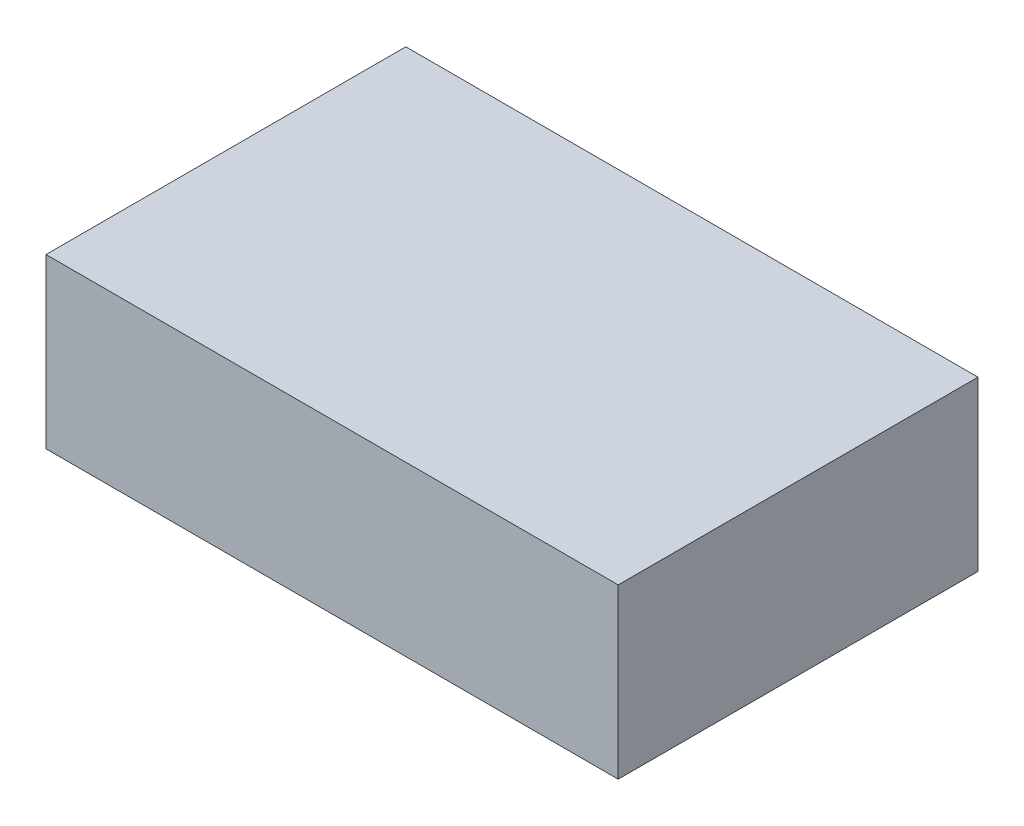
SolidWorks part; units mm, degrees
ref_plane "前视基准面" through (0, 0, 0) normal (0, 0, 1) x (1, 0, 0)
ref_plane "上视基准面" through (0, 0, 0) normal (0, 1, 0) x (1, 0, 0)
ref_plane "右视基准面" through (0, 0, 0) normal (1, 0, 0) x (0, 0, -1)
sketch "草图1" plane through (0, 0, 0) normal (0, 1, 0) x (1, 0, 0)
  line L1 (0, 0) -> (98.6, 0)
  line L2 (0, 0) -> (0, -62)
  line L3 (0, -62) -> (98.6, -62)
  line L4 (98.6, 0) -> (98.6, -62)
  dimension "D1" = 98.6
  dimension "D2" = 62
extrude "凸台-拉伸1" add sketch "草图1" along normal blind 29
ref_plane "基准面1" through (0, 0, 31) normal (0, 0, 1) x (1, 0, 0)
ref_plane "基准面2" through (0, 14.5, 0) normal (0, 1, 0) x (1, 0, 0)
ref_plane "基准面3" through (49.3, 0, 0) normal (1, 0, 0) x (0, 0, -1)
